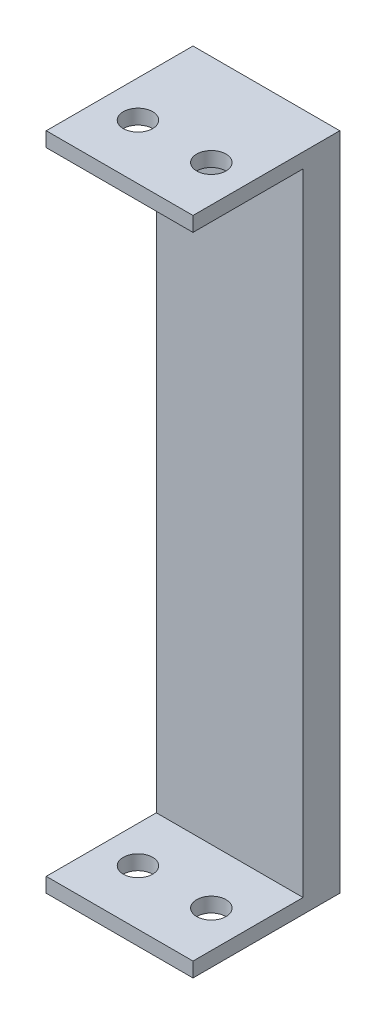
SolidWorks part; units mm, degrees
material "ABS"
ref_plane "Front Plane" through (0, 0, 0) normal (0, 0, 1) x (1, 0, 0)
ref_plane "Top Plane" through (0, 0, 0) normal (0, 1, 0) x (1, 0, 0)
ref_plane "Right Plane" through (0, 0, 0) normal (1, 0, 0) x (0, 0, -1)
sketch "Sketch1" plane through (0, 0, 0) normal (0, 0, 1) x (1, 0, 0)
  line L1 (-10, -45) -> (10, -45)
  line L2 (-10, -45) -> (-10, 45)
  line L3 (-10, 45) -> (10, 45)
  line L4 (10, -45) -> (10, 45)
  line L5 (-10, -45) -> (10, 45) construction
  line L6 (-10, 45) -> (10, -45) construction
  point P0 (0, 0)
  dimension "D1" = 90
  dimension "D2" = 20
extrude "Boss-Extrude1" add sketch "Sketch1" along normal blind 20
sketch "Sketch2" plane through (10, 0, 0) normal (1, 0, 0) x (0, 0, -1)
  line L0 (-20, 43) -> (-5, 43)
  line L1 (-20, -45) -> (-20, 45) construction
  line L2 (-5, 43) -> (-5, -43)
  line L3 (-5, -43) -> (-20, -43)
  line L4 (-20, -43) -> (-20, 43)
  line L5 (-20, 45) -> (0, 45) construction
  line L6 (0, -45) -> (0, 45) construction
  line L7 (-20, -45) -> (0, -45) construction
  dimension "D1" = 2
  dimension "D2" = 5
  dimension "D3" = 2
extrude "Cut-Extrude1" cut sketch "Sketch2" against normal up to next
sketch "Sketch3" plane through (0, 45, 0) normal (0, 1, 0) x (1, 0, 0)
  line L0 (-20.7542, -12.5) -> (31.839, -12.5) construction
  line L1 (-5, 5.3789) -> (-5, -31.1118) construction
  line L2 (5, 5.3789) -> (5, -31.1118) construction
  line L5 (10, -20) -> (-10, -20) construction
  line L7 (-10, -20) -> (-10, 0) construction
  line L8 (10, -20) -> (10, 0) construction
  circle A0 centre (-5, -12.5) radius 2
  circle A1 centre (5, -12.5) radius 2
  dimension "D4" = 4
  dimension "D5" = 4
  dimension "D1" = 7.5
  dimension "D2" = 5
  dimension "D3" = 5
extrude "Cut-Extrude2" cut sketch "Sketch3" against normal blind 140 and the other way through all
